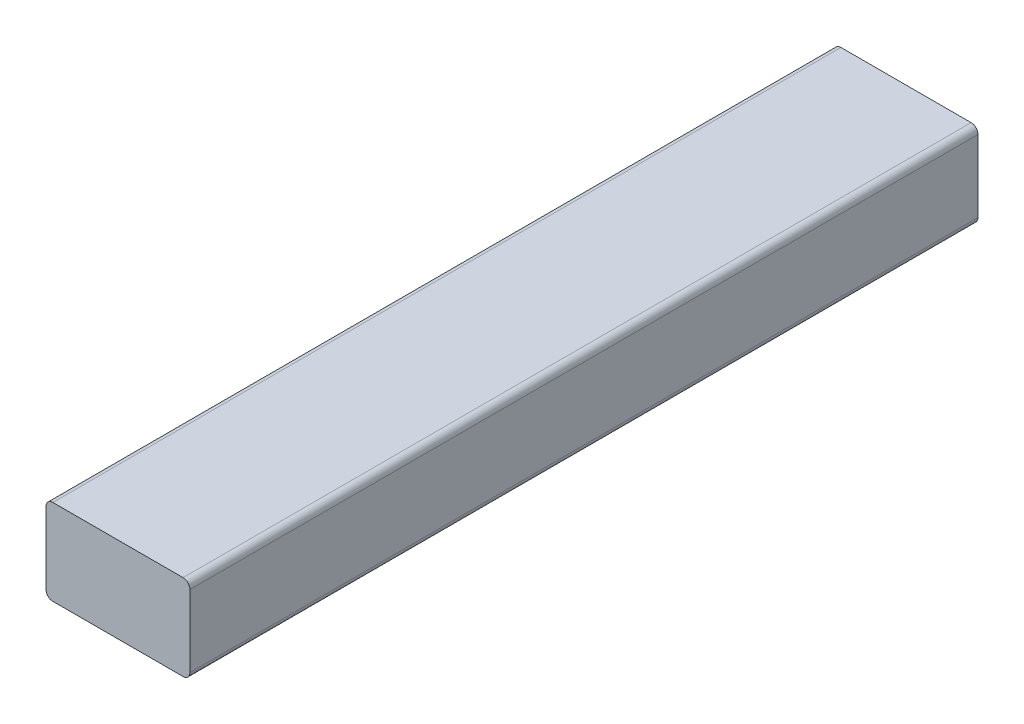
SolidWorks part; units mm, degrees
material "Polyurethane Foam Rigid"
ref_plane "Front Plane" through (0, 0, 0) normal (0, 0, 1) x (1, 0, 0)
ref_plane "Top Plane" through (0, 0, 0) normal (0, 1, 0) x (1, 0, 0)
ref_plane "Right Plane" through (0, 0, 0) normal (1, 0, 0) x (0, 0, -1)
sketch "Sketch1" plane through (0, 0, 0) normal (0, 0, 1) x (1, 0, 0)
  line L1 (-29.3403, 15.8854) -> (12.6597, 15.8854)
  line L2 (-29.3403, 15.8854) -> (-29.3403, -9.1146)
  line L3 (-29.3403, -9.1146) -> (12.6597, -9.1146)
  line L4 (12.6597, 15.8854) -> (12.6597, -9.1146)
  dimension "D1" = 25
  dimension "D2" = 42
extrude "Boss-Extrude1" add sketch "Sketch1" against normal blind 230
fillet "Fillet1" radius 2 4 edges at (12.6597, -9.1146, -115) (12.6597, 15.8854, -115) (-29.3403, -9.1146, -115) (-29.3403, 15.8854, -115)
